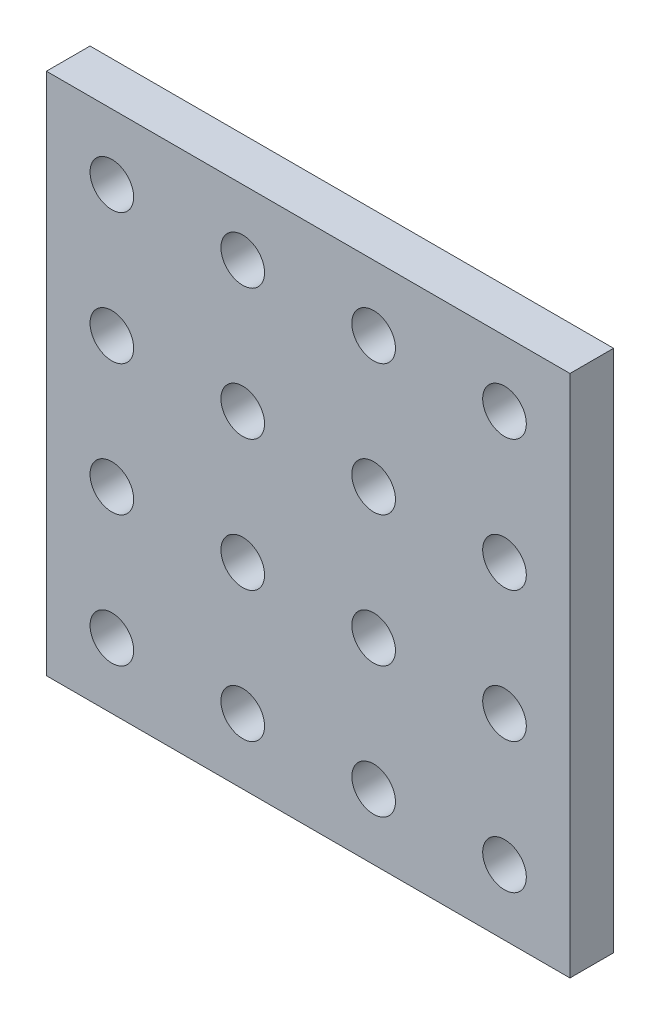
SolidWorks part; units mm, degrees
ref_plane "Front Plane" through (0, 0, 0) normal (0, 0, 1) x (1, 0, 0)
ref_plane "Top Plane" through (0, 0, 0) normal (0, 1, 0) x (1, 0, 0)
ref_plane "Right Plane" through (0, 0, 0) normal (1, 0, 0) x (0, 0, -1)
sketch "Sketch1" plane through (0, 0, 0) normal (0, 0, 1) x (1, 0, 0)
  line L0 (0, 0) -> (120, 0)
  line L1 (120, 0) -> (120, 120)
  line L2 (120, 120) -> (0, 120)
  line L3 (0, 120) -> (0, 0)
  circle A0 centre (15, 105) radius 5
  circle A1 centre (45, 105) radius 5
  circle A2 centre (75, 105) radius 5
  circle A3 centre (105, 105) radius 5
  circle A4 centre (45, 75) radius 5
  circle A5 centre (75, 75) radius 5
  circle A6 centre (105, 75) radius 5
  circle A7 centre (45, 45) radius 5
  circle A8 centre (75, 45) radius 5
  circle A9 centre (105, 45) radius 5
  circle A10 centre (45, 15) radius 5
  circle A11 centre (75, 15) radius 5
  circle A12 centre (105, 15) radius 5
  circle A13 centre (15, 75) radius 5
  circle A14 centre (15, 45) radius 5
  circle A15 centre (15, 15) radius 5
  dimension "D5" = 10
  dimension "D8" = 30
  dimension "D9" = 30
  dimension "D1" = 120
  dimension "D2" = 120
  dimension "D3" = 15
  dimension "D4" = 15
  dimension "D6" = 4
  dimension "D7" = 4
extrude "Boss-Extrude1" add sketch "Sketch1" along normal blind 10
